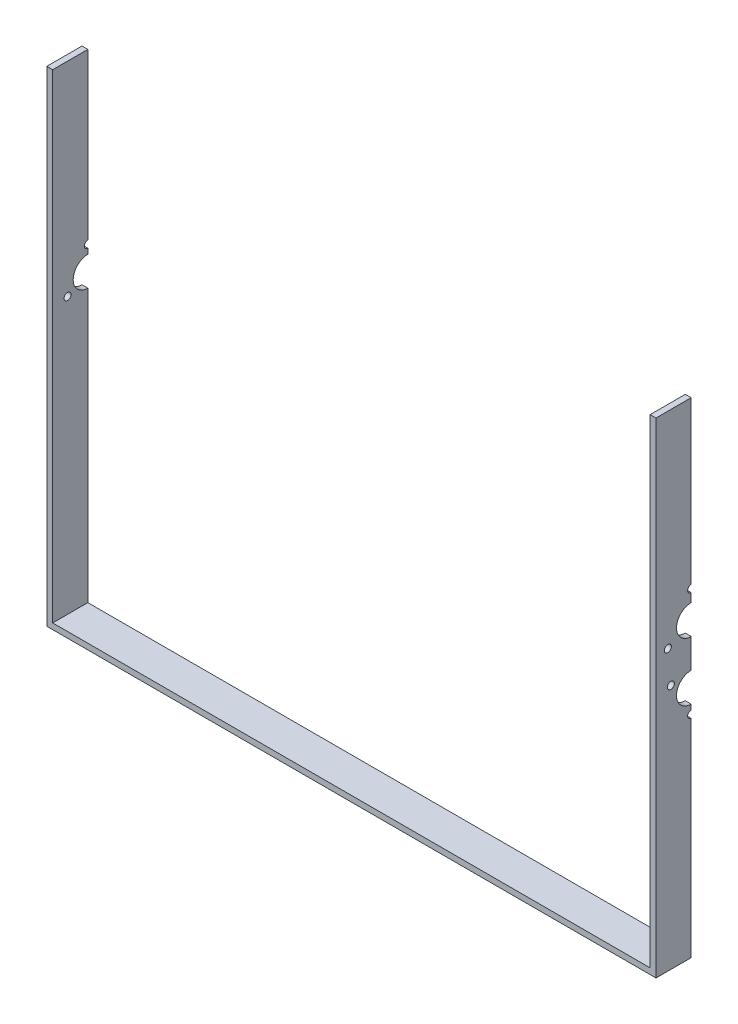
SolidWorks part; units mm, degrees
material "普通碳钢"
ref_plane "前视基准面" through (0, 0, 0) normal (0, 0, 1) x (1, 0, 0)
ref_plane "上视基准面" through (0, 0, 0) normal (0, 1, 0) x (1, 0, 0)
ref_plane "右视基准面" through (0, 0, 0) normal (1, 0, 0) x (0, 0, -1)
sketch "草图1" plane through (0, 0, 0) normal (0, 0, 1) x (1, 0, 0)
  line L1 (-255, -204.5) -> (255, -204.5)
  line L2 (-255, -204.5) -> (-255, 204.5)
  line L3 (-255, 204.5) -> (255, 204.5) construction
  line L4 (255, -204.5) -> (255, 204.5)
  line L5 (-255, -204.5) -> (255, 204.5) construction
  line L6 (-255, 204.5) -> (255, -204.5) construction
  point P0 (0, 0)
  dimension "D1" = 510
  dimension "D2" = 409
extrude "拉伸-薄壁1" add sketch "草图1" along normal blind 30 thin
sketch "草图2" plane through (-260, 0, 0) normal (-1, 0, 0) x (0, 0, 1)
  line L0 (0, -209.5) -> (0, 204.5) construction
  line L1 (30, -209.5) -> (0, -209.5) construction
  circle A0 centre (0, 40.5) radius 12.5
  circle A1 centre (0, -9.5) radius 12.5 construction
  dimension "D1" = 250
  dimension "D2" = 50
  dimension "D3" = 25
  dimension "D4" = 25
extrude "切除-拉伸1" cut sketch "草图2" against normal up to next
sketch "草图3" plane through (260, 0, 0) normal (1, 0, 0) x (0, 0, -1)
  line L1 (0, 204.5) -> (0, -209.5) construction
  circle A0 centre (0, 40.5) radius 12.5
  circle A1 centre (0, -9.5) radius 12.5
  dimension "D1" = 25
  dimension "D2" = 25
  dimension "D3" = 50
extrude "切除-拉伸2" cut sketch "草图3" against normal up to next
sketch "草图4" plane through (0, 0, 0) normal (0, 0, -1) x (-1, 0, 0)
  line L0 (-294.1384, -109.5) -> (357.6753, -109.5) construction
  line L1 (-260, -209.5) -> (260, -209.5) construction
  line L2 (0, -204.5) -> (0, 0) construction
  line L3 (260, -209.5) -> (260, 28) construction
  line L4 (280, -94.5) -> (260, -94.5)
  line L5 (280, -124.5) -> (260, -124.5)
  line L6 (-255, -204.5) -> (255, -204.5) construction
  line L7 (-280, -124.5) -> (-260, -124.5)
  line L8 (-280, -94.5) -> (-260, -94.5)
  line L9 (-255, 15.5) -> (91.4834, 15.5) construction
  line L10 (-255, 28) -> (-255, 3) construction
  line L11 (280, 155.5) -> (260, 155.5)
  line L12 (280, 125.5) -> (260, 125.5)
  line L13 (-280, 125.5) -> (-260, 125.5)
  line L14 (-280, 155.5) -> (-260, 155.5)
  line L15 (260, -94.5) -> (260, -124.5)
  line L16 (260, 155.5) -> (260, 125.5)
  line L17 (-260, -94.5) -> (-260, -124.5)
  line L18 (-260, 155.5) -> (-260, 125.5)
  circle A0 centre (280, -109.5) radius 5
  arc A1 (280, -124.5) -> (280, -94.5) centre (280, -109.5) ccw
  circle A2 centre (-280, -109.5) radius 5
  arc A3 (-280, -124.5) -> (-280, -94.5) centre (-280, -109.5) cw
  circle A4 centre (280, 140.5) radius 5
  arc A5 (280, 155.5) -> (280, 125.5) centre (280, 140.5) cw
  circle A6 centre (-280, 140.5) radius 5
  arc A7 (-280, 155.5) -> (-280, 125.5) centre (-280, 140.5) ccw
  dimension "D2" = 15
  dimension "D3" = 10
  dimension "D1" = 100
  dimension "D4" = 20
extrude "凸台-拉伸1" [suppressed] add sketch "草图4" against normal blind 5
sketch "草图5" plane through (260, 0, 0) normal (1, 0, 0) x (0, 0, -1)
  circle A0 centre (0, -9.5) radius 20 construction
  circle A1 centre (0, -29.5) radius 3
  circle A2 centre (-17.3205, 0.5) radius 3
  circle A3 centre (17.3205, 0.5) radius 3 construction
  point P11 (0, -9.5)
  dimension "D1" = 40
  dimension "D2" = 6
  dimension "D3" = 3
extrude "切除-拉伸3" cut sketch "草图5" against normal up to surface (5 mm away) up to face at (255, 7.75, 10.625)
sketch "草图6" plane through (-260, 0, 0) normal (-1, 0, 0) x (0, 0, 1)
  circle A0 centre (0, 40.5) radius 20 construction
  circle A1 centre (0, 60.5) radius 3
  circle A2 centre (17.3205, 30.5) radius 3
  circle A3 centre (-17.3205, 30.5) radius 3 construction
  point P12 (0, 40.5)
  dimension "D1" = 40
  dimension "D2" = 6
  dimension "D3" = 3
extrude "切除-拉伸5" cut sketch "草图6" against normal up to surface (5 mm away) up to face at (-255, 13.5, 12.0833)
sketch "草图7" plane through (260, 0, 0) normal (1, 0, 0) x (0, 0, -1)
  circle A0 centre (0, 40.5) radius 23 construction
  circle A1 centre (0, 63.5) radius 3
  circle A2 centre (19.9186, 29) radius 3 construction
  circle A3 centre (-19.9186, 29) radius 3
  point P11 (0, 40.5)
  dimension "D1" = 46
  dimension "D2" = 6
  dimension "D3" = 3
extrude "切除-拉伸6" cut sketch "草图7" against normal up to surface (5 mm away) up to face at (255, 0.5, 14.3205)
